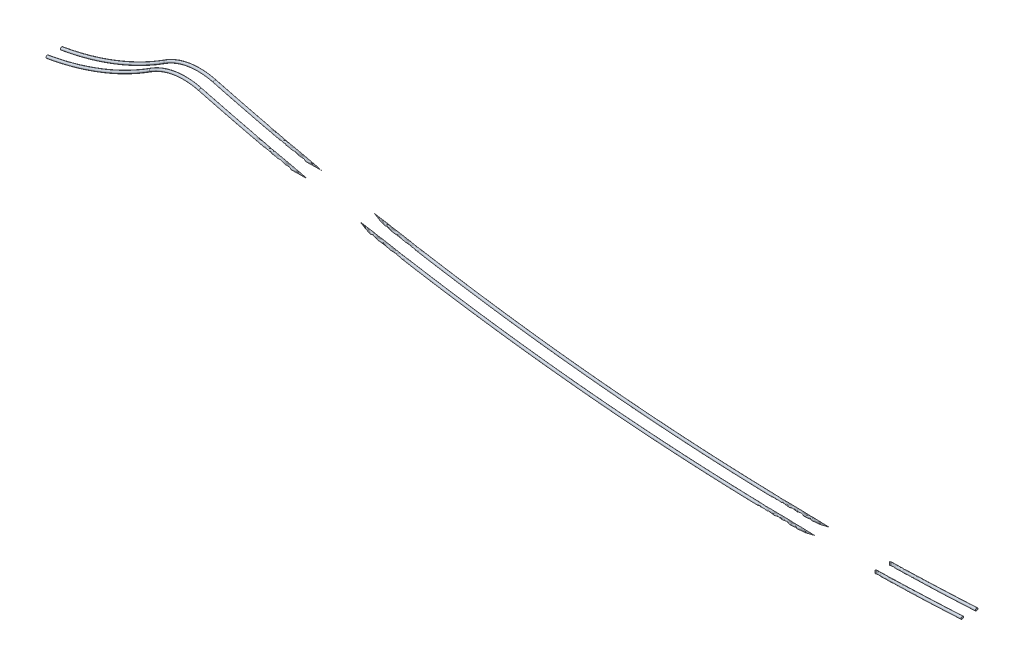
SolidWorks part; units mm, degrees
ref_plane "前基準面" through (0, 0, 0) normal (0, 0, 1) x (1, 0, 0)
ref_plane "上基準面" through (0, 0, 0) normal (0, 1, 0) x (1, 0, 0)
ref_plane "右基準面" through (0, 0, 0) normal (1, 0, 0) x (0, 0, -1)
sketch "草圖1" plane through (0, 0, 0) normal (0, 0, 1) x (1, 0, 0)
  line L0 (50.8818, 27.8378) -> (110.2059, 27.8378) construction
  line L1 (0, 0) -> (500, 0) construction
  line L2 (0, 0) -> (0, 120.8101) construction
  line L3 (0, 120.8101) -> (500, 120.8101) construction
  line L4 (500, 0) -> (500, 120.8101) construction
  line L5 (508.7698, -15.8177) -> (466.1286, -15.8177) construction
  arc A0 (0, 0) -> (57.6224, 22.3894) centre (-26.7747, 154.2531) ccw
  arc A1 (57.6224, 22.3894) -> (85.0036, 26.7081) centre (76.242, -6.7024) cw
  arc A2 (85.0036, 26.7081) -> (508.7698, -15.8177) centre (431.6864, 1348.715) ccw
  dimension "D1" = 500
sketch "草圖2" plane through (0, 0, 0) normal (1, 0, 0) x (0, 0, -1)
  line L0 (4, 0) -> (-4, 0) construction
  circle A0 centre (-4, 0) radius 0.75
  circle A1 centre (4, 0) radius 0.75
  point P4 (0, 0)
  dimension "D1" = 1.5
  dimension "D2" = 8
sweep "掃出1" add profiles "草圖2" path "草圖1"
